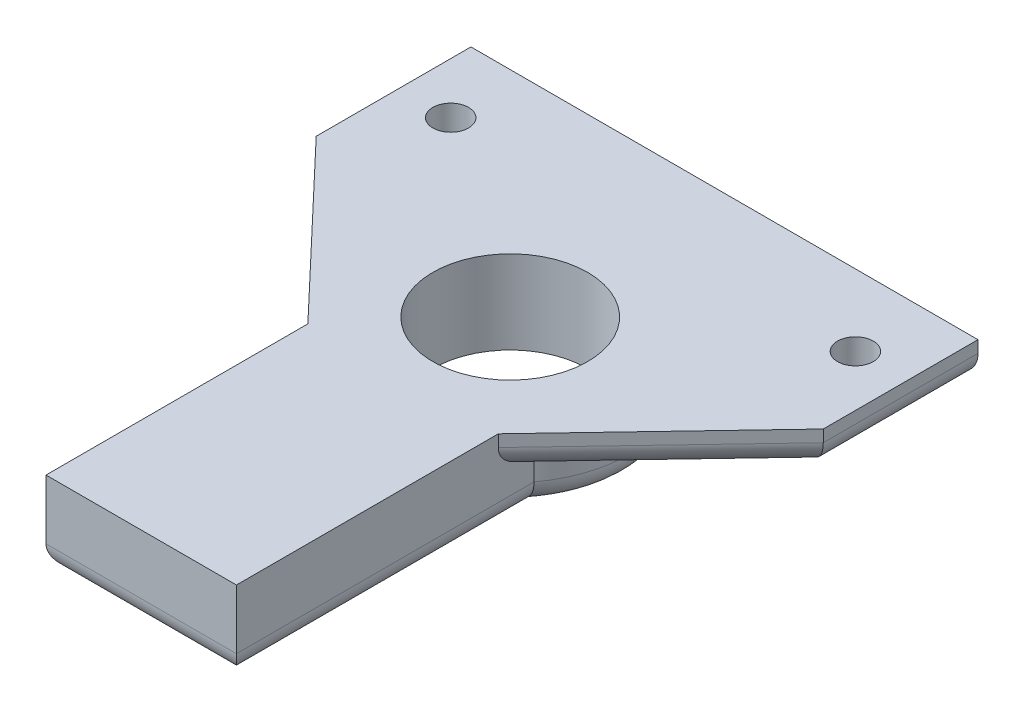
SolidWorks part; units mm, degrees
ref_plane "Front Plane" through (0, 0, 0) normal (0, 0, 1) x (1, 0, 0)
ref_plane "Top Plane" through (0, 0, 0) normal (0, 1, 0) x (1, 0, 0)
ref_plane "Right Plane" through (0, 0, 0) normal (1, 0, 0) x (0, 0, -1)
sketch "Sketch1" plane through (0, 0, 0) normal (0, 1, 0) x (1, 0, 0)
  line L0 (-10.65, 18) -> (-4, 11)
  line L1 (4, 0) -> (-4, 0)
  line L4 (-4, 0) -> (-4, 11)
  line L5 (4, 11) -> (4, 0)
  line L11 (-10.65, 18) -> (-10.65, 24.5)
  line L12 (-10.65, 24.5) -> (10.65, 24.5)
  line L13 (10.65, 24.5) -> (10.65, 18)
  line L14 (10.65, 18) -> (4, 11)
  point P0 (0, 0)
  point P5 (-4, 7.8619)
  point P9 (0, 0)
  point P10 (0, 24.5)
  dimension "D1" = 24.5
  dimension "D2" = 8
  dimension "D3" = 6.5
  dimension "D4" = 21.3
  dimension "D5" = 11
extrude "Boss-Extrude1" add sketch "Sketch1" along normal blind 1.5
sketch "Sketch2" plane through (0, 0, 0) normal (0, -1, 0) x (1, 0, 0)
  line L0 (4, 0) -> (4, -11) construction
  line L1 (-4, -11) -> (-4, 0) construction
  line L2 (-4, 0) -> (4, 0) construction
  line L3 (4, 0) -> (4, -12.5)
  line L4 (-4, -12.5) -> (-4, 0)
  line L5 (-4, 0) -> (4, 0)
  line L6 (10.65, -24.5) -> (-10.65, -24.5) construction
  arc A0 (-4, -12.5) -> (4, -12.5) centre (0, -15.5) ccw
  point P6 (0, 0)
  point P8 (0, 0)
  point P9 (0, 0)
  point P10 (0, 0)
  point P11 (4, -11.576)
  point P13 (-4, -12.053)
  point P15 (0, 0)
  dimension "D1" = 9
  dimension "D2" = 5
extrude "Boss-Extrude2" add sketch "Sketch2" along normal blind 2
fillet "Fillet1" radius 1 4 edges at (4, -2, -6.25) (0, -2, -20.5) (-4, -2, -6.25) (0, -2, 0)
fillet "Fillet2" radius 1 4 edges at (10.65, 0, -21.25) (7.325, 0, -14.5) (-7.325, 0, -14.5) (-10.65, 0, -21.25)
sketch "Sketch3" plane through (0, -2, 0) normal (0, -1, 0) x (1, 0, 0)
  circle A0 centre (0, -15.5) radius 3.25
  dimension "D1" = 6.5
extrude "Cut-Extrude1" cut sketch "Sketch3" against normal through all
sketch "Sketch4" plane through (0, 0, 0) normal (0, -1, 0) x (1, 0, 0)
  line L0 (0, 0) -> (0, -50000) construction
  line L1 (9.65, -24.5) -> (-9.65, -24.5) construction
  circle A0 centre (-8.5, -21.5) radius 0.75
  circle A1 centre (8.5, -21.5) radius 0.75
  point P7 (0, 0)
  dimension "D1" = 1.5
  dimension "D2" = 17
  dimension "D3" = 3
extrude "Cut-Extrude2" cut sketch "Sketch4" against normal through all
